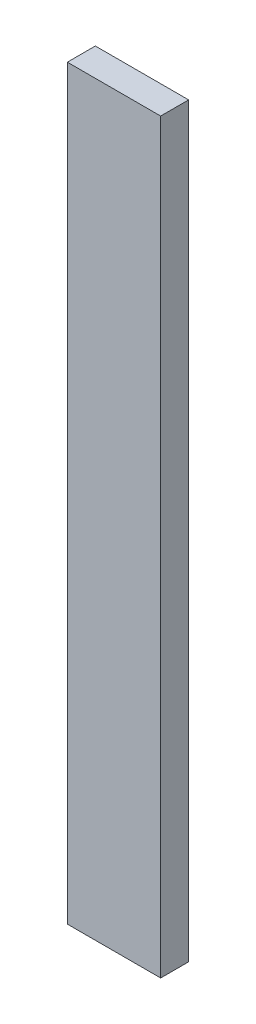
SolidWorks part; units mm, degrees
ref_plane "Front Plane" through (0, 0, 0) normal (0, 0, 1) x (1, 0, 0)
ref_plane "Top Plane" through (0, 0, 0) normal (0, 1, 0) x (1, 0, 0)
ref_plane "Right Plane" through (0, 0, 0) normal (1, 0, 0) x (0, 0, -1)
sketch "Sketch1" plane through (0, 0, 0) normal (0, 0, 1) x (1, 0, 0)
  line L1 (-5, 40) -> (5, 40)
  line L2 (-5, 40) -> (-5, -40)
  line L3 (-5, -40) -> (5, -40)
  line L4 (5, 40) -> (5, -40)
  line L5 (-5, 40) -> (5, -40) construction
  line L6 (-5, -40) -> (5, 40) construction
  point P0 (0, 0)
  dimension "D1" = 80
  dimension "D2" = 10
extrude "Boss-Extrude1" add sketch "Sketch1" along normal blind 3
